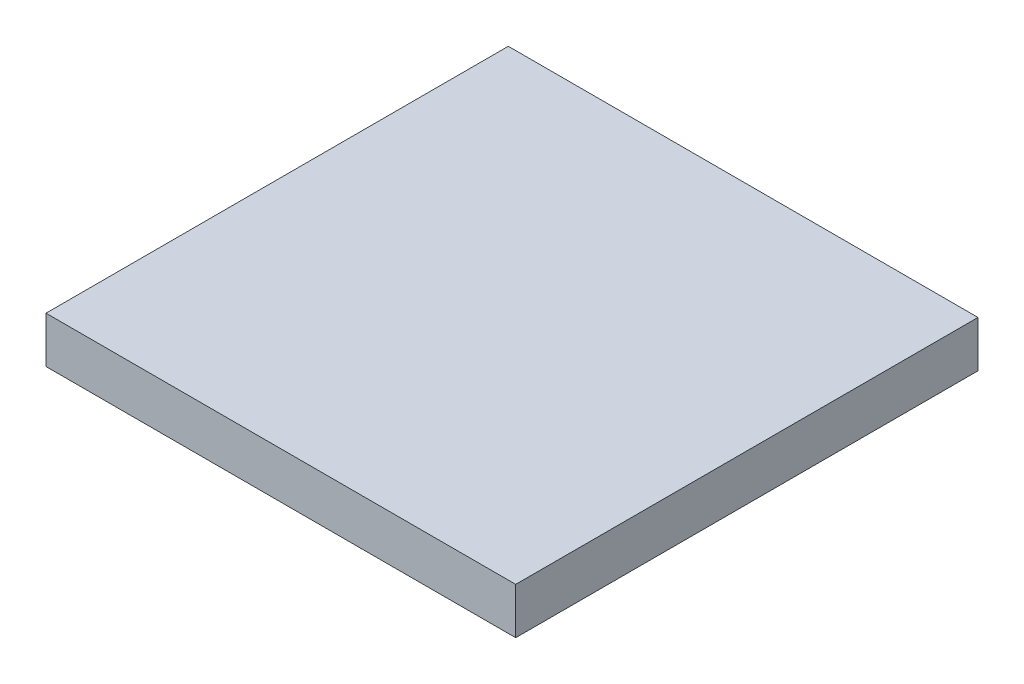
SolidWorks part; units mm, degrees
ref_plane "Front Plane" through (0, 0, 0) normal (0, 0, 1) x (1, 0, 0)
ref_plane "Top Plane" through (0, 0, 0) normal (0, 1, 0) x (1, 0, 0)
ref_plane "Right Plane" through (0, 0, 0) normal (1, 0, 0) x (0, 0, -1)
sketch "Sketch1" plane through (0, 0, 0) normal (0, 1, 0) x (1, 0, 0)
  line L1 (-25.4, -25) -> (25.4, -25)
  line L2 (-25.4, -25) -> (-25.4, 25)
  line L3 (-25.4, 25) -> (25.4, 25)
  line L4 (25.4, -25) -> (25.4, 25)
  line L5 (-25.4, -25) -> (25.4, 25) construction
  line L6 (-25.4, 25) -> (25.4, -25) construction
  point P0 (0, 0)
  dimension "D1" = 50.8
  dimension "D2" = 50
extrude "Boss-Extrude1" add sketch "Sketch1" along normal blind 5
